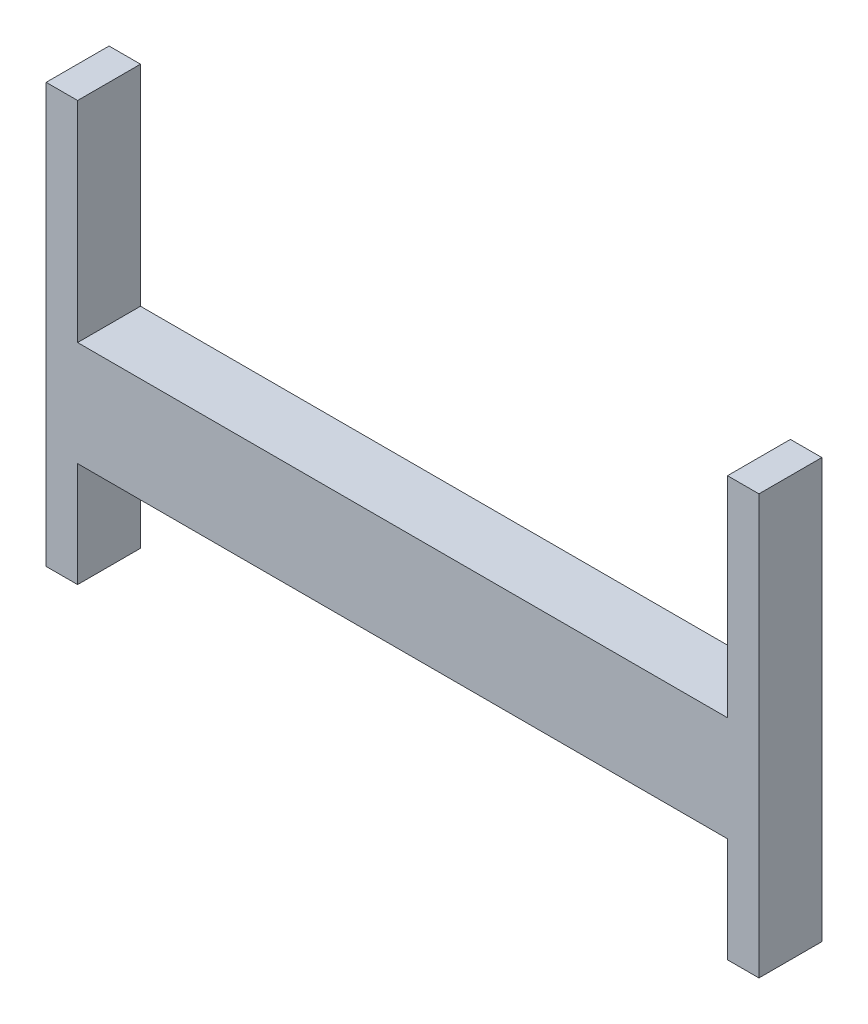
SolidWorks part; units mm, degrees
ref_plane "Alzado" through (0, 0, 0) normal (0, 0, 1) x (1, 0, 0)
ref_plane "Planta" through (0, 0, 0) normal (0, 1, 0) x (1, 0, 0)
ref_plane "Vista lateral" through (0, 0, 0) normal (1, 0, 0) x (0, 0, -1)
sketch "Croquis1" plane through (0, 0, 0) normal (0, 0, 1) x (1, 0, 0)
  line L0 (-170, -25) -> (-155, -25) construction
  line L5 (155, -25) -> (-155, -25)
  line L11 (155, 25) -> (-155, 25)
  line L14 (155, -25) -> (-155, 25) construction
  line L15 (155, 25) -> (-155, -25) construction
  line L21 (-155, 25) -> (-155, 125)
  line L22 (-155, 125) -> (-170, 125)
  line L23 (-170, -25) -> (-170, 125)
  line L25 (-170, -25) -> (-170, -75)
  line L26 (-170, -75) -> (-155, -75)
  line L27 (-155, -25) -> (-155, -75)
  line L28 (-155, 25) -> (-155, -25) construction
  line L29 (155, 25) -> (155, -25) construction
  line L30 (0, 75.5227) -> (0, -50.1198) construction
  line L31 (155, 125) -> (170, 125)
  line L32 (170, -75) -> (155, -75)
  line L33 (155, -25) -> (155, -75)
  line L34 (170, -25) -> (170, -75)
  line L35 (155, 25) -> (155, 125)
  line L36 (170, -25) -> (170, 125)
  point P0 (0, 0)
  point P17 (0, 0)
  dimension "D1" = 310
  dimension "D2" = 50
  dimension "D3" = 150
  dimension "D4" = 50
  dimension "D5" = 15
extrude "Saliente-Extruir1" add sketch "Croquis1" along normal blind 30
